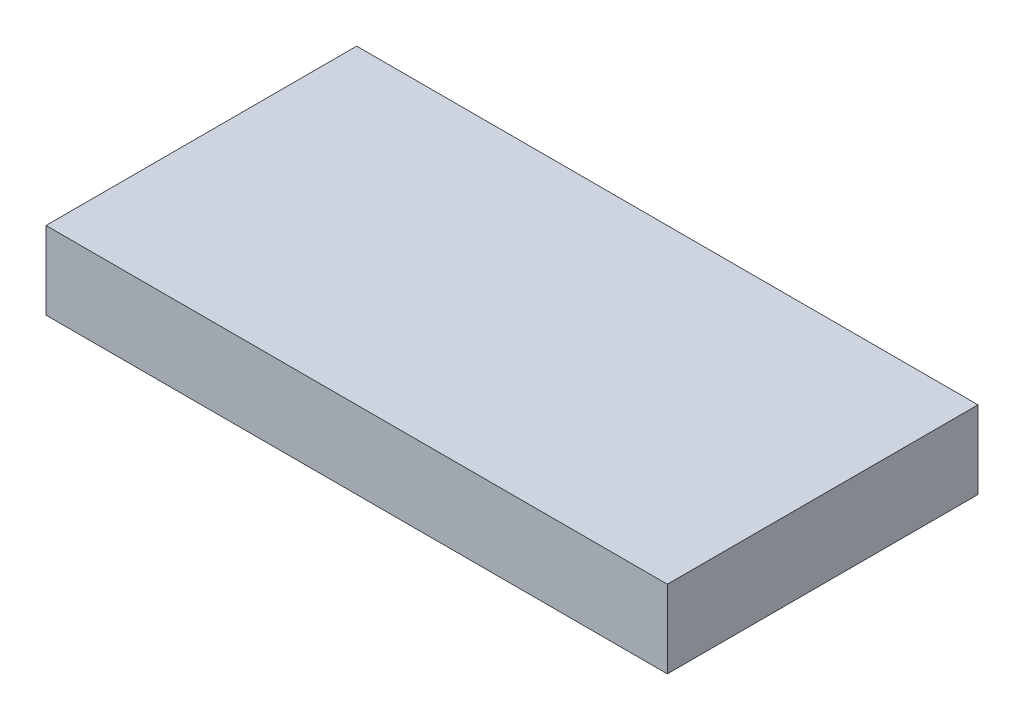
SolidWorks part; units mm, degrees
ref_plane "Front Plane" through (0, 0, 0) normal (0, 0, 1) x (1, 0, 0)
ref_plane "Top Plane" through (0, 0, 0) normal (0, 1, 0) x (1, 0, 0)
ref_plane "Right Plane" through (0, 0, 0) normal (1, 0, 0) x (0, 0, -1)
sketch "Sketch1" plane through (0, 0, 0) normal (0, 1, 0) x (1, 0, 0)
  line L1 (-64.547, 29.9487) -> (95.453, 29.9487)
  line L2 (-64.547, 29.9487) -> (-64.547, -50.0513)
  line L3 (-64.547, -50.0513) -> (95.453, -50.0513)
  line L4 (95.453, 29.9487) -> (95.453, -50.0513)
  dimension "D1" = 160
  dimension "D2" = 80
extrude "Boss-Extrude1" add sketch "Sketch1" along normal blind 20
